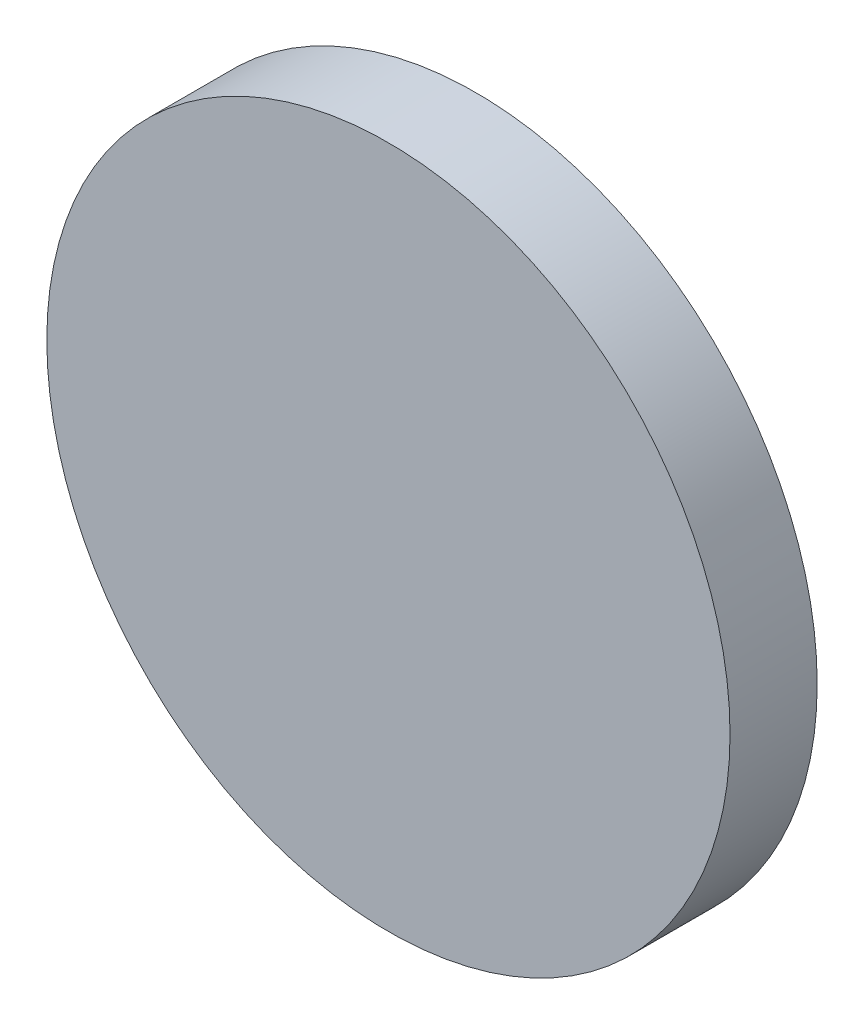
SolidWorks part; units mm, degrees
ref_plane "Front Plane" through (0, 0, 0) normal (0, 0, 1) x (1, 0, 0)
ref_plane "Top Plane" through (0, 0, 0) normal (0, 1, 0) x (1, 0, 0)
ref_plane "Right Plane" through (0, 0, 0) normal (1, 0, 0) x (0, 0, -1)
sketch "Sketch1" plane through (0, 0, 0) normal (0, 0, 1) x (1, 0, 0)
  circle A0 centre (0, 0) radius 12.446
  dimension "D1" = 24.892
extrude "Boss-Extrude1" add sketch "Sketch1" along normal blind 3.175
